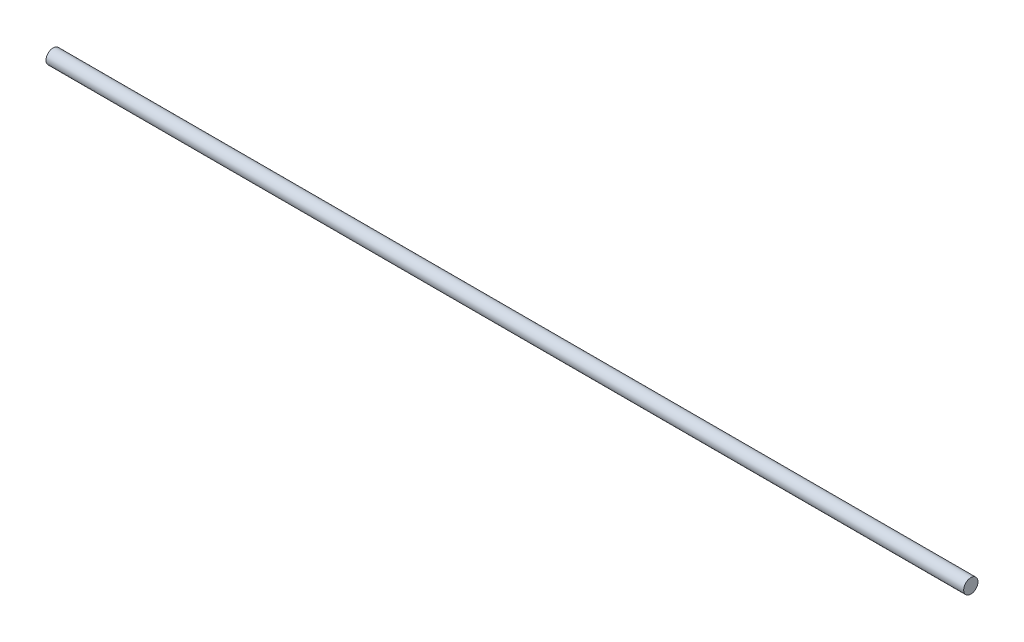
SolidWorks part; units mm, degrees
ref_plane "Front Plane" through (0, 0, 0) normal (0, 0, 1) x (1, 0, 0)
ref_plane "Top Plane" through (0, 0, 0) normal (0, 1, 0) x (1, 0, 0)
ref_plane "Right Plane" through (0, 0, 0) normal (1, 0, 0) x (0, 0, -1)
sketch "Sketch1" plane through (0, 0, 0) normal (1, 0, 0) x (0, 0, -1)
  circle A0 centre (0, 0) radius 3.9687
  dimension "D1" = 7.9375
extrude "Boss-Extrude1" add sketch "Sketch1" along normal blind 508
